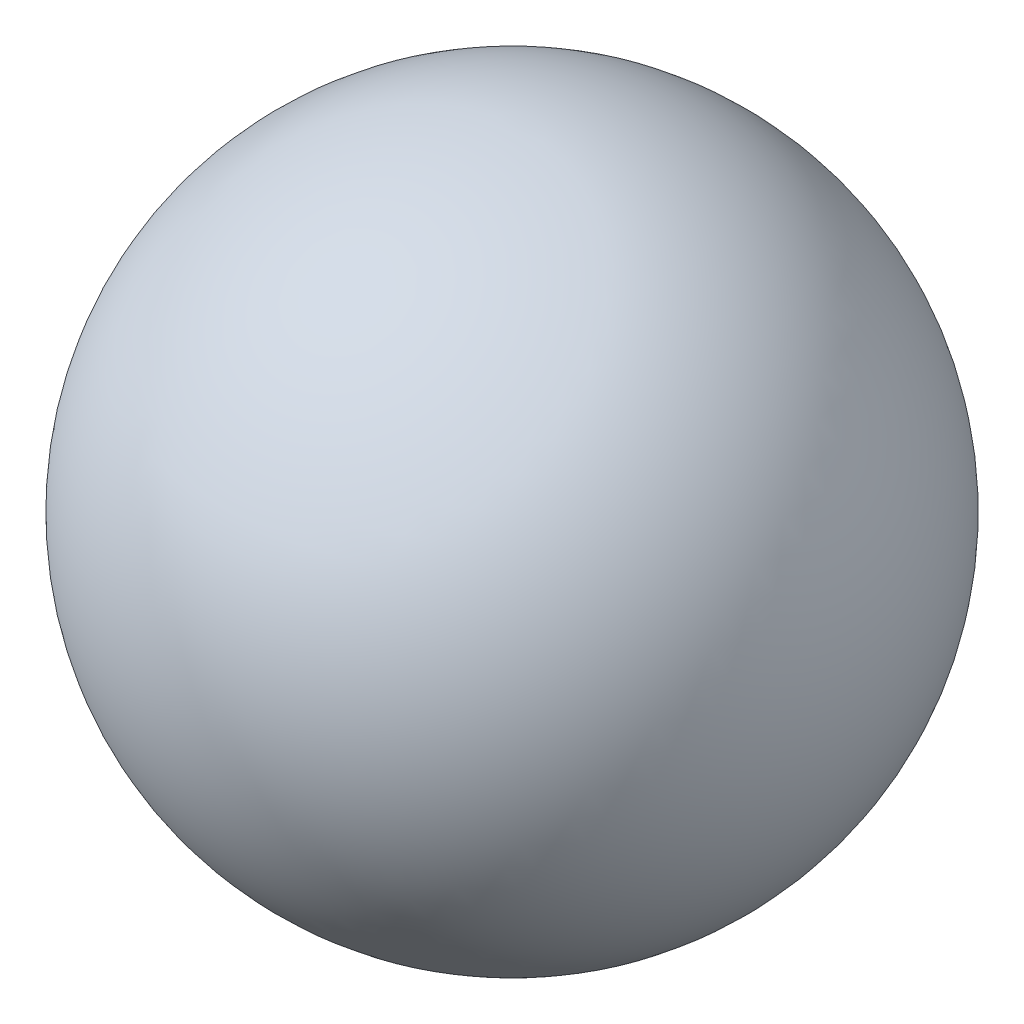
SolidWorks part; units mm, degrees
material "PE Low/Medium Density"
ref_plane "Front Plane" through (0, 0, 0) normal (0, 0, 1) x (1, 0, 0)
ref_plane "Top Plane" through (0, 0, 0) normal (0, 1, 0) x (1, 0, 0)
ref_plane "Right Plane" through (0, 0, 0) normal (1, 0, 0) x (0, 0, -1)
sketch "Sketch1" plane through (0, 0, 0) normal (0, 0, 1) x (1, 0, 0)
  line L0 (0, 5.8112) -> (0, -8.3512) construction
  line L1 (0, 1.27) -> (0, -1.27)
  line L2 (0, 1.27) -> (0, -1.27)
  arc A0 (0, -1.27) -> (0, 1.27) centre (0, 0) ccw
  dimension "D1" = 1.27
revolve "Revolve1" add sketch "Sketch1" angle 360 about L0
